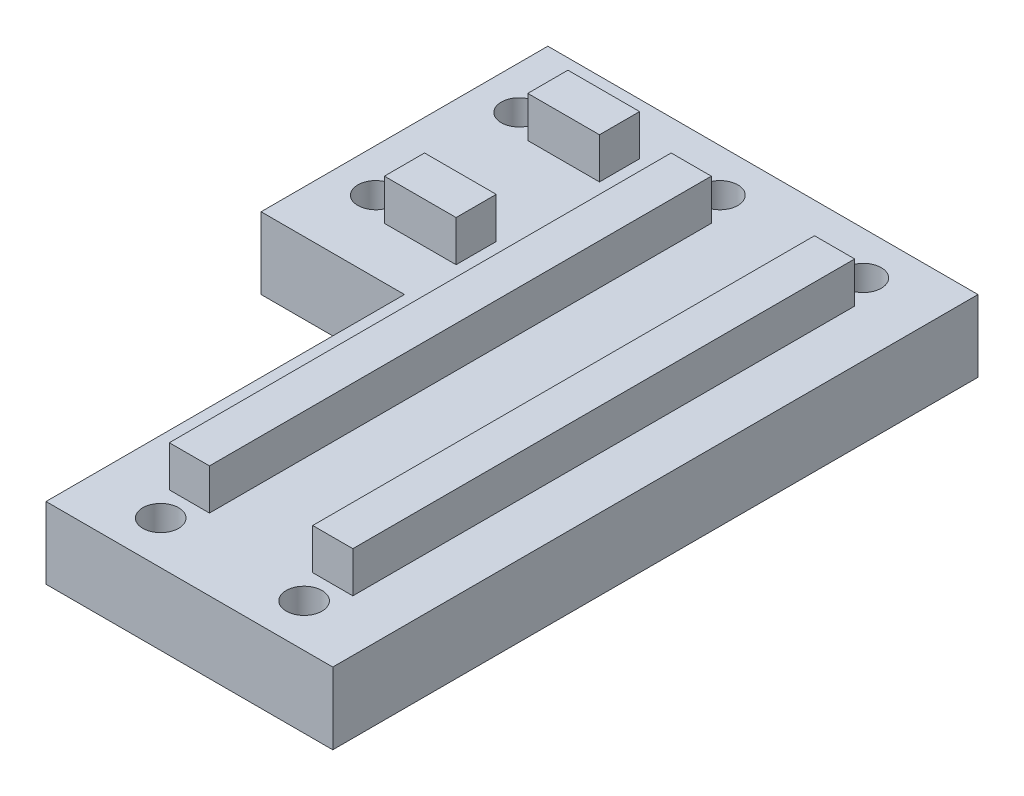
SolidWorks part; units mm, degrees
ref_plane "Alzado" through (0, 0, 0) normal (0, 0, 1) x (1, 0, 0)
ref_plane "Planta" through (0, 0, 0) normal (0, 1, 0) x (1, 0, 0)
ref_plane "Vista lateral" through (0, 0, 0) normal (1, 0, 0) x (0, 0, -1)
sketch "Croquis1" plane through (0, 0, 0) normal (0, 1, 0) x (1, 0, 0)
  line L1 (25, 20) -> (-65, 20)
  line L2 (25, 20) -> (25, -20)
  line L3 (-15, -20) -> (-65, -20)
  line L4 (-65, 20) -> (-65, -20)
  line L8 (25, -20) -> (25, -70)
  line L9 (25, -70) -> (-15, -70)
  line L10 (-15, -20) -> (-15, -70)
  point P0 (0, 0)
  dimension "D1" = 40
  dimension "D2" = 90
  dimension "D3" = 40
  dimension "D4" = 50
extrude "Saliente-Extruir1" add sketch "Croquis1" along normal blind 10
sketch "Croquis2" plane through (0, 0, 70) normal (0, 0, 1) x (1, 0, 0)
  line L27 (25, 10) -> (25, 0) construction
  line B0 (15, 15.7) -> (15, 1.4751) construction
  line B1 (12.2, 9.9874) -> (12.2, 15.7)
  line B2 (17.8, 15.7) -> (17.8, 9.9874)
  line B3 (15, 9.9874) -> (12.2, 9.9874)
  line B4 (12.2, 15.7) -> (17.8, 15.7)
  line B5 (17.8, 9.9874) -> (15, 9.9874)
  line B6 (-5, 15.7) -> (-5, 1.4751) construction
  line B7 (-7.8, 9.9874) -> (-7.8, 15.7)
  line B8 (-2.2, 15.7) -> (-2.2, 9.9874)
  line B9 (-5, 9.9874) -> (-7.8, 9.9874)
  line B10 (-7.8, 15.7) -> (-2.2, 15.7)
  line B11 (-2.2, 9.9874) -> (-5, 9.9874)
  dimension "D1" = 10
  dimension "D2" = 2
  dimension "D3" = 20
sketch_block_instance "Bloque1-1"
sketch_block "Bloque1" parameters "D1"=1.5, "D2"=4.6406
sketch_block_instance "Bloque1-2"
extrude "Saliente-Extruir2" add sketch "Croquis2" against normal through all
sketch "Croquis3" plane through (-65, 0, 0) normal (-1, 0, 0) x (0, 0, 1)
  line L13 (20, 10) -> (20, 0) construction
  line B0 (10, 15.7) -> (10, 10) construction
  line B1 (7.2, 10) -> (7.2, 15.7)
  line B2 (12.8, 15.7) -> (12.8, 10)
  line B3 (10, 10) -> (7.2, 10)
  line B4 (7.2, 15.7) -> (12.8, 15.7)
  line B5 (12.8, 10) -> (10, 10)
  line B6 (-12.8, 10) -> (-12.8, 15.7)
  line B7 (-7.2, 15.7) -> (-7.2, 10)
  line B8 (-10, 10) -> (-12.8, 10)
  line B9 (-12.8, 15.7) -> (-7.2, 15.7)
  line B10 (-7.2, 10) -> (-10, 10)
  dimension "D1" = 10
  dimension "D2" = 2
  dimension "D3" = 20
sketch_block_instance "Bloque2-1"
sketch_block "Bloque2" parameters "D1"=1.5, "D2"=6.3541
sketch_block_instance "Bloque2-2"
extrude "Saliente-Extruir3" add sketch "Croquis3" against normal blind 50
sketch "Croquis6" plane through (-65, 0, 0) normal (-1, 0, 0) x (0, 0, 1)
  line L1 (-28.4643, 27.9616) -> (28.4643, 27.9616)
  line L2 (-28.4643, 27.9616) -> (-28.4643, -27.9616)
  line L3 (-28.4643, -27.9616) -> (28.4643, -27.9616)
  line L4 (28.4643, 27.9616) -> (28.4643, -27.9616)
  line L5 (-28.4643, 27.9616) -> (28.4643, -27.9616) construction
  line L6 (-28.4643, -27.9616) -> (28.4643, 27.9616) construction
extrude "Cortar-Extruir2" cut sketch "Croquis6" against normal blind 30
sketch "Croquis5" plane through (0, 15.7, 0) normal (0, 1, 0) x (1, 0, 0)
  line L0 (-15, -20) -> (-15, -70) construction
  line L1 (-15, -70) -> (25, -70)
  line L2 (-15, -70) -> (-15, -60)
  line L3 (-15, -60) -> (25, -60)
  line L4 (25, -70) -> (25, -60)
  line L5 (25, -70) -> (25, 20) construction
  line L24 (25, -70) -> (25, 20) construction
  line L25 (25, 20) -> (-15, 20)
  line L26 (25, 20) -> (25, 10)
  line L27 (25, 10) -> (-15, 10)
  line L28 (-15, 20) -> (-15, 10)
  line L29 (12.2, 20) -> (-2.2, 20) construction
  line L31 (-2.2, -70) -> (12.2, -70) construction
  line L32 (-35, -7.2) -> (-35, 7.2) construction
  line L33 (-25, 20) -> (-35, 20)
  line L34 (-25, 20) -> (-25, -20)
  line L35 (-25, -20) -> (-35, -20)
  line L36 (-35, 20) -> (-35, -20)
  line L37 (-25, 20) -> (-35, -20) construction
  line L38 (-25, -20) -> (-35, 20) construction
  line L39 (-7.8, 20) -> (-35, 20) construction
  line L40 (-35, -20) -> (-15, -20) construction
  point P14 (-30, 0)
  dimension "D1" = 10
  dimension "10" = 10
  dimension "D3" = 10
extrude "Cortar-Extruir1" cut sketch "Croquis5" against normal up to surface (5.7 mm away) up to face at (-22.5429, 10, 10)
sketch "Croquis7" plane through (0, 10, 0) normal (0, 1, 0) x (1, 0, 0)
  line L0 (-35, -20) -> (-15, -20) construction
  line L1 (-15, -20) -> (-15, -70) construction
  line L2 (25, -70) -> (25, 20) construction
  line L3 (-35, -20) -> (-35, 20) construction
  line L4 (-15, -70) -> (25, -70) construction
  line L5 (25, 20) -> (-35, 20) construction
  circle A0 centre (-29, 10) radius 2.5
  circle A1 centre (-29, -10) radius 2.5
  circle A2 centre (15, 14) radius 2.5
  circle A3 centre (-5, 14) radius 2.5
  circle A4 centre (-5, -64) radius 2.5
  circle A5 centre (15, -64) radius 2.5
  dimension "D1" = 5
  dimension "D2" = 10
  dimension "D3" = 20
  dimension "D4" = 10
  dimension "D5" = 20
  dimension "D6" = 10
  dimension "D7" = 20
  dimension "D8" = 6
  dimension "D9" = 6
  dimension "D10" = 6
extrude "Cortar-Extruir3" cut sketch "Croquis7" against normal through all
